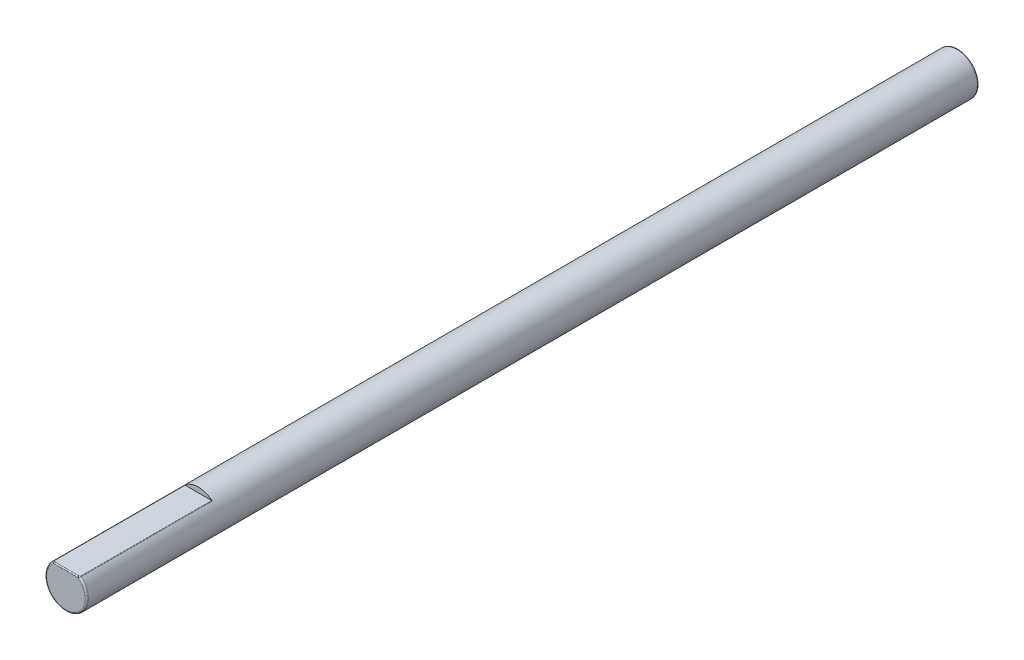
SolidWorks part; units mm, degrees
ref_plane "Front Plane" through (0, 0, 0) normal (0, 0, 1) x (1, 0, 0)
ref_plane "Top Plane" through (0, 0, 0) normal (0, 1, 0) x (1, 0, 0)
ref_plane "Right Plane" through (0, 0, 0) normal (1, 0, 0) x (0, 0, -1)
sketch "Sketch1" plane through (0, 0, 0) normal (0, 0, 1) x (1, 0, 0)
  circle A0 centre (0, 0) radius 1.5773
  dimension "D1" = 3.1547
extrude "Boss-Extrude1" add sketch "Sketch1" along normal blind 67.564
fillet "Fillet1" radius 0.127 2 edges at (1.5773, 0, 0) (1.5773, 0, 67.564)
sketch "Sketch2" plane through (0, 0, 0) normal (1, 0, 0) x (0, 0, -1)
  line L0 (-0.127, 1.5773) -> (-67.437, 1.5773) construction
  line L1 (-67.564, 1.4503) -> (-67.564, -1.4503) construction
  line L2 (-57.531, 1.5773) -> (-67.437, 1.5773)
  line L3 (-67.564, 1.4503) -> (-67.564, 1.1963)
  line L4 (-57.531, 1.1963) -> (-67.564, 1.1963)
  line L5 (-0.127, 1.1963) -> (-67.183, 1.1963) construction
  line L6 (-67.183, 1.1963) -> (-67.183, -1.4503) construction
  line L7 (-57.531, 1.5773) -> (-57.531, 1.1963)
  line L8 (-67.564, 1.4503) -> (-67.564, -1.4503) construction
  line L10 (-0.127, 1.5773) -> (-67.437, 1.5773) construction
  arc A0 (-67.437, 1.5773) -> (-67.564, 1.4503) centre (-67.437, 1.4503) ccw construction
  arc A1 (-67.437, 1.5773) -> (-67.564, 1.4503) centre (-67.437, 1.4503) ccw
  arc A2 (-67.183, 1.1963) -> (-67.183, 1.1963) centre (-67.183, 1.1963) ccw
  dimension "D2" = 10.033
  dimension "D1" = 0.381
extrude "Cut-Extrude1" cut sketch "Sketch2" against normal through all and the other way through all contours L2 A1 L3 L4 L7
fillet "Fillet2" radius 0.0762 5 edges at (-1.028, 1.1963, 62.484) (1.028, 1.1963, 62.484) (-0.5857, 1.1963, 67.3908) (1.0048, 1.1963, 67.4969) (0, 1.1963, 67.564)
